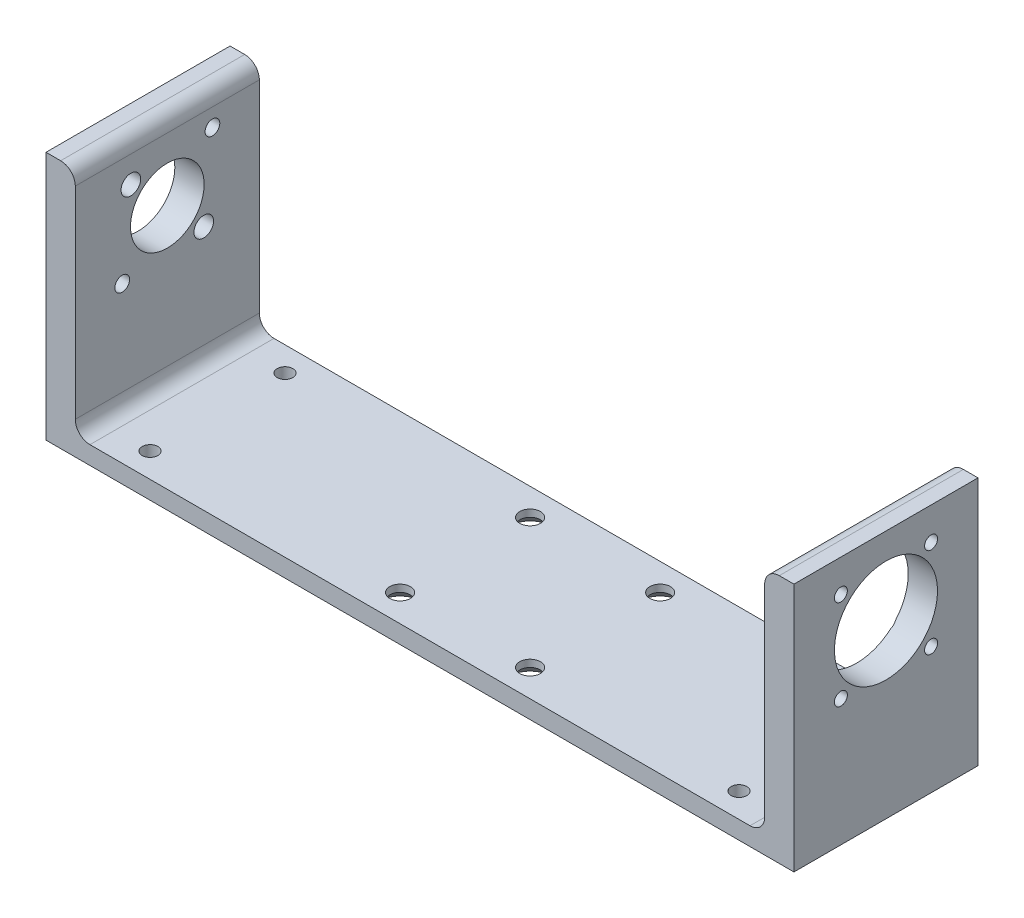
SolidWorks part; units mm, degrees
ref_plane "Front" through (0, 0, 0) normal (0, 0, 1) x (1, 0, 0)
ref_plane "Top" through (0, 0, 0) normal (0, 1, 0) x (1, 0, 0)
ref_plane "Right" through (0, 0, 0) normal (1, 0, 0) x (0, 0, -1)
sketch "Sketch1" plane through (0, 0, 0) normal (0, 0, 1) x (1, 0, 0)
  line L0 (-140.462, 101.6) -> (-152.4, 101.6)
  line L1 (-152.4, 101.6) -> (-152.4, 0)
  line L2 (-152.4, 0) -> (152.4, 0)
  line L3 (152.4, 0) -> (152.4, 101.6)
  line L4 (152.4, 101.6) -> (140.462, 101.6)
  line L5 (140.462, 101.6) -> (140.462, 7.366)
  line L6 (140.462, 7.366) -> (-140.462, 7.366)
  line L7 (-140.462, 7.366) -> (-140.462, 101.6)
  dimension "Leg THickness" = 11.938
  dimension "BaseThickness" = 7.366
  dimension "LegLength" = 101.6
  dimension "BaseWidth" = 304.8
extrude "Boss-Extrude1" add sketch "Sketch1" along normal mid plane 75
fillet "Fillet1" radius 5.969 4 edges at (140.462, 101.6, 0) (-140.462, 101.6, 0) (-140.462, 7.366, 0) (140.462, 7.366, 0)
sketch "Sketch2" plane through (152.4, 0, 0) normal (1, 0, 0) x (0, 0, -1)
  line L0 (0, 0) -> (0, 70) construction
  circle A0 centre (0, 70) radius 26 construction
  circle A1 centre (0, 70) radius 21
  dimension "D1" = 52
  dimension "D2" = 42
  dimension "D3" = 70
extrude "Cut-Extrude1" cut sketch "Sketch2" against normal blind 21
sketch "Sketch3" plane through (140.462, 0, 0) normal (-1, 0, 0) x (0, 0, 1)
  line L0 (0, 70) -> (18.3848, 88.3848) construction
  line L1 (0, 70) -> (12.2165, 70) construction
  circle A0 centre (0, 70) radius 26 construction
  circle A1 centre (0, 70) radius 26 construction
  dimension "D1" = 45
hole_wizard "CSK for M5 Flat Head Machine Screw1" positions "3DSketch1" profile "Sketch4" countersink size "M5" standard "ANSI Metric"
sketch3d "3DSketch1"
  point P0 (140.462, 88.3848, 18.3848)
sketch "Sketch4" plane through (140.462, 88.3848, 18.3848) normal (0, 1, 0) x (0, 0, 1)
  line L0 (0, 0) -> (0, 20.5923)
  line L1 (0, 20.5923) -> (2.65, 19)
  line L2 (2.65, 19) -> (2.65, 2.55)
  line L3 (2.65, 2.55) -> (5.2, 0)
  line L5 (5.2, 0) -> (0, 0)
  line L6 (-2.65, 2.55) -> (-5.2, 0) construction
  line L10 (0, 20.5923) -> (-2.65, 19) construction
  line L11 (0, -6.35) -> (0, 107.95) construction
  dimension "Hole Dia." = 5.3
  dimension "Hole Depth" = 19
  dimension "Near C'Sink Dia." = 10.4
  dimension "Near C'Sink Angle" = 90
  dimension "Drill Angle" = 118
pattern_circular "CirPattern1" count 4 over 360 about axis through (0, 70, 0) along (1, 0, 0) of "CSK for M5 Flat Head Machine Screw1"
sketch "Sketch5" plane through (-140.462, 0, 0) normal (1, 0, 0) x (0, 0, -1)
  circle A0 centre (0, 70) radius 15
  dimension "D1" = 30
extrude "Cut-Extrude2" cut sketch "Sketch5" against normal blind 21
sketch "Sketch6" plane through (0, 0, 0) normal (0, -1, 0) x (1, 0, 0)
  circle A0 centre (33.8734, -26.5) radius 3.5 construction
  circle A1 centre (-19.1266, -26.5) radius 3.5 construction
  circle A2 centre (33.8734, 26.5) radius 3.5 construction
  circle A3 centre (-19.1266, 26.5) radius 3.5 construction
  circle A4 centre (33.8734, -26.5) radius 3.5
  circle A5 centre (-19.1266, -26.5) radius 3.5
  circle A6 centre (33.8734, 26.5) radius 3.5
  circle A7 centre (-19.1266, 26.5) radius 3.5
hole_wizard "CSK for M8 Flat Head Machine Screw1" positions "3DSketch3" profile "Sketch8" countersink size "M8" standard "ANSI Metric"
sketch3d "3DSketch3"
  point P0 (-19.1266, 0, 26.5)
  point P3 (33.8734, 0, 26.5)
  point P6 (33.8734, 0, -26.5)
  point P9 (-19.1266, 0, -26.5)
sketch "Sketch8" plane through (-19.1266, 0, 26.5) normal (1, 0, 0) x (0, 0, -1)
  line L0 (0, 0) -> (0, 15.2236)
  line L1 (0, 15.2236) -> (4.2, 12.7)
  line L2 (4.2, 12.7) -> (4.2, 4.45)
  line L3 (4.2, 4.45) -> (8.65, 0)
  line L5 (8.65, 0) -> (0, 0)
  line L6 (-4.2, 4.45) -> (-8.65, 0) construction
  line L10 (0, 15.2236) -> (-4.2, 12.7) construction
  line L11 (0, -6.35) -> (0, 107.95) construction
  dimension "Hole Dia." = 8.4
  dimension "Hole Depth" = 12.7
  dimension "Near C'Sink Dia." = 17.3
  dimension "Near C'Sink Angle" = 90
  dimension "Drill Angle" = 118
sketch "Sketch10" plane through (0, 0, 0) normal (0, -1, 0) x (1, 0, 0)
  line L1 (-120, -27.5) -> (120, -27.5) construction
  line L2 (-120, -27.5) -> (-120, 27.5) construction
  line L3 (-120, 27.5) -> (120, 27.5) construction
  line L4 (120, -27.5) -> (120, 27.5) construction
  line L5 (-120, -27.5) -> (120, 27.5) construction
  line L6 (-120, 27.5) -> (120, -27.5) construction
  point P0 (0, 0)
  dimension "D1" = 55
  dimension "D2" = 240
hole_wizard "M6 Clearance Hole1" positions "3DSketch4" profile "Sketch12" hole size "M6" standard "ANSI Metric"
sketch3d "3DSketch4"
  point P0 (-120, 0, 27.5)
  point P4 (120, 0, 27.5)
  point P7 (120, 0, -27.5)
  point P10 (-120, 0, -27.5)
sketch "Sketch12" plane through (-120, 0, 27.5) normal (1, 0, 0) x (0, 0, -1)
  line L0 (0, 0) -> (0, 14.6228)
  line L1 (0, 14.6228) -> (3.2, 12.7)
  line L2 (3.2, 12.7) -> (3.2, 0)
  line L5 (3.2, 0) -> (0, 0)
  line L10 (0, 14.6228) -> (-3.2, 12.7) construction
  line L11 (0, -6.35) -> (0, 107.95) construction
  dimension "Hole Dia." = 6.4
  dimension "Hole Depth" = 12.7
  dimension "Drill Angle" = 118
sketch "Sketch13" plane through (-152.4, 0, 0) normal (-1, 0, 0) x (0, 0, 1)
  line L0 (0, 70) -> (-18.3848, 88.3848) construction
  line L1 (0, 70) -> (0, 80.79) construction
  line L2 (-304.8, 70) -> (-286.4152, 51.6152) construction
  line L3 (0, 70) -> (18.3848, 51.6152) construction
  line L4 (0, 70) -> (-14.8492, 55.1508) construction
  line L5 (0, 70) -> (14.8492, 84.8492) construction
  circle A3 centre (-18.3848, 88.3848) radius 3
  circle A4 centre (18.3848, 51.6152) radius 3
  circle A5 centre (-14.8492, 55.1508) radius 4
  circle A6 centre (14.8492, 84.8492) radius 4
  dimension "D6" = 6
  dimension "D7" = 8
  dimension "D1" = 45
  dimension "D2" = 26
  dimension "D5" = 21
  dimension "D3" = 2
  dimension "D4" = 2
extrude "Cut-Extrude3" cut sketch "Sketch13" against normal up to surface (11.938 mm away) up to face at (-140.462, 85, 0)
equation "\"D1@Fillet1\" = \"Leg THickness@Sketch1\"/2"
